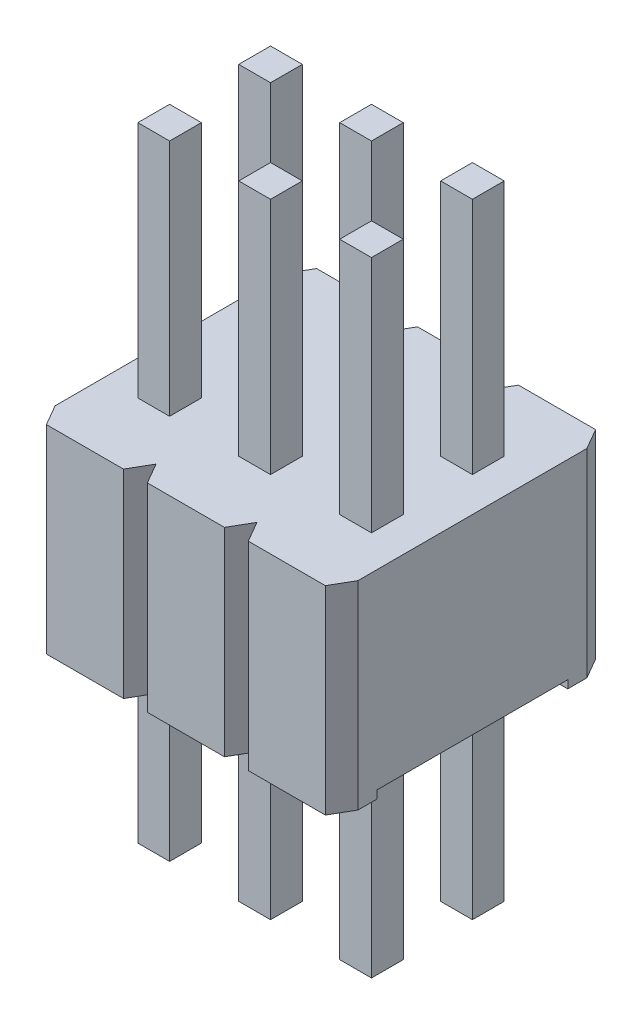
SolidWorks part; units mm, degrees
ref_plane "Front Plane" through (0, 0, 0) normal (0, 0, 1) x (1, 0, 0)
ref_plane "Top Plane" through (0, 0, 0) normal (0, 1, 0) x (1, 0, 0)
ref_plane "Right Plane" through (0, 0, 0) normal (1, 0, 0) x (0, 0, -1)
ref_plane "Plane1" through (0, 2.5, 0) normal (0, 1, 0) x (1, 0, 0)
sketch "Sketch1" plane through (0, 2.5, 0) normal (0, 1, 0) x (1, 0, 0)
  line L0 (3.175, -1.7) -> (3.175, 1.7)
  line L1 (3.175, 1.7) -> (-0.635, 1.7)
  line L2 (-0.635, 1.7) -> (-0.635, -1.7)
  line L3 (-0.635, -1.7) -> (3.175, -1.7)
extrude "Boss-Extrude1" add sketch "Sketch1" against normal blind 2.5
sketch "Sketch2" plane through (0, 0, 0) normal (0, -1, 0) x (1, 0, 0)
  line L0 (0.785, 1.7) -> (0.485, 1.7)
  line L1 (0.485, 1.7) -> (0.635, 1.44)
  line L2 (0.635, 1.44) -> (0.785, 1.7)
extrude "Cut-Extrude1" cut sketch "Sketch2" against normal blind 2.5
sketch "Sketch3" plane through (0, 0, 0) normal (0, -1, 0) x (1, 0, 0)
  line L0 (1.755, -1.7) -> (2.055, -1.7)
  line L1 (2.055, -1.7) -> (1.905, -1.44)
  line L2 (1.905, -1.44) -> (1.755, -1.7)
extrude "Cut-Extrude2" cut sketch "Sketch3" against normal blind 2.5
sketch "Sketch4" plane through (0, 0, 0) normal (0, -1, 0) x (1, 0, 0)
  line L0 (0.485, -1.7) -> (0.785, -1.7)
  line L1 (0.785, -1.7) -> (0.635, -1.44)
  line L2 (0.635, -1.44) -> (0.485, -1.7)
extrude "Cut-Extrude3" cut sketch "Sketch4" against normal blind 2.5
sketch "Sketch5" plane through (3.175, 0, 0) normal (1, 0, 0) x (0, 0, -1)
  line L0 (1.2, 0) -> (1.2, 0.1)
  line L1 (1.2, 0.1) -> (-1.2, 0.1)
  line L2 (-1.2, 0.1) -> (-1.2, 0)
  line L3 (-1.2, 0) -> (1.2, 0)
extrude "Cut-Extrude4" cut sketch "Sketch5" against normal through all
sketch "Sketch6" plane through (0, 0, 0) normal (0, -1, 0) x (1, 0, 0)
  line L0 (2.055, 1.7) -> (1.755, 1.7)
  line L1 (1.755, 1.7) -> (1.905, 1.44)
  line L2 (1.905, 1.44) -> (2.055, 1.7)
extrude "Cut-Extrude5" cut sketch "Sketch6" against normal blind 2.5
sketch "Sketch7" plane through (0, 0.1, 0) normal (0, -1, 0) x (1, 0, 0)
  line L0 (2.34, 0.835) -> (2.74, 0.835)
  line L1 (2.74, 0.835) -> (2.74, 0.435)
  line L2 (2.74, 0.435) -> (2.34, 0.435)
  line L3 (2.34, 0.435) -> (2.34, 0.835)
extrude "Boss-Extrude2" add sketch "Sketch7" along normal blind 2.45
sketch "Sketch8" plane through (0, 0.1, 0) normal (0, -1, 0) x (1, 0, 0)
  line L0 (2.34, -0.835) -> (2.34, -0.435)
  line L1 (2.34, -0.435) -> (2.74, -0.435)
  line L2 (2.74, -0.435) -> (2.74, -0.835)
  line L3 (2.74, -0.835) -> (2.34, -0.835)
extrude "Boss-Extrude3" add sketch "Sketch8" along normal blind 2.45
sketch "Sketch9" plane through (0, 0.1, 0) normal (0, -1, 0) x (1, 0, 0)
  line L0 (1.07, 0.835) -> (1.47, 0.835)
  line L1 (1.47, 0.835) -> (1.47, 0.435)
  line L2 (1.47, 0.435) -> (1.07, 0.435)
  line L3 (1.07, 0.435) -> (1.07, 0.835)
extrude "Boss-Extrude4" add sketch "Sketch9" along normal blind 2.45
sketch "Sketch10" plane through (0, 0.1, 0) normal (0, -1, 0) x (1, 0, 0)
  line L0 (1.07, -0.835) -> (1.07, -0.435)
  line L1 (1.07, -0.435) -> (1.47, -0.435)
  line L2 (1.47, -0.435) -> (1.47, -0.835)
  line L3 (1.47, -0.835) -> (1.07, -0.835)
extrude "Boss-Extrude5" add sketch "Sketch10" along normal blind 2.45
sketch "Sketch11" plane through (0, 0.1, 0) normal (0, -1, 0) x (1, 0, 0)
  line L0 (-0.2, 0.835) -> (0.2, 0.835)
  line L1 (0.2, 0.835) -> (0.2, 0.435)
  line L2 (0.2, 0.435) -> (-0.2, 0.435)
  line L3 (-0.2, 0.435) -> (-0.2, 0.835)
extrude "Boss-Extrude6" add sketch "Sketch11" along normal blind 2.45
sketch "Sketch12" plane through (0, 0.1, 0) normal (0, -1, 0) x (1, 0, 0)
  line L0 (-0.2, -0.835) -> (-0.2, -0.435)
  line L1 (-0.2, -0.435) -> (0.2, -0.435)
  line L2 (0.2, -0.435) -> (0.2, -0.835)
  line L3 (0.2, -0.835) -> (-0.2, -0.835)
extrude "Boss-Extrude7" add sketch "Sketch12" along normal blind 2.45
sketch "Sketch13" plane through (0, 2.5, 0) normal (0, 1, 0) x (-1, 0, 0)
  line L0 (-2.74, 0.835) -> (-2.34, 0.835)
  line L1 (-2.34, 0.835) -> (-2.34, 0.435)
  line L2 (-2.34, 0.435) -> (-2.74, 0.435)
  line L3 (-2.74, 0.435) -> (-2.74, 0.835)
extrude "Boss-Extrude8" add sketch "Sketch13" along normal blind 3
sketch "Sketch14" plane through (0, 2.5, 0) normal (0, 1, 0) x (-1, 0, 0)
  line L0 (-2.34, -0.435) -> (-2.34, -0.835)
  line L1 (-2.34, -0.835) -> (-2.74, -0.835)
  line L2 (-2.74, -0.835) -> (-2.74, -0.435)
  line L3 (-2.74, -0.435) -> (-2.34, -0.435)
extrude "Boss-Extrude9" add sketch "Sketch14" along normal blind 3
sketch "Sketch15" plane through (0, 2.5, 0) normal (0, 1, 0) x (-1, 0, 0)
  line L0 (-1.47, 0.835) -> (-1.07, 0.835)
  line L1 (-1.07, 0.835) -> (-1.07, 0.435)
  line L2 (-1.07, 0.435) -> (-1.47, 0.435)
  line L3 (-1.47, 0.435) -> (-1.47, 0.835)
extrude "Boss-Extrude10" add sketch "Sketch15" along normal blind 3
sketch "Sketch16" plane through (0, 2.5, 0) normal (0, 1, 0) x (-1, 0, 0)
  line L0 (-1.07, -0.435) -> (-1.07, -0.835)
  line L1 (-1.07, -0.835) -> (-1.47, -0.835)
  line L2 (-1.47, -0.835) -> (-1.47, -0.435)
  line L3 (-1.47, -0.435) -> (-1.07, -0.435)
extrude "Boss-Extrude11" add sketch "Sketch16" along normal blind 3
sketch "Sketch17" plane through (0, 2.5, 0) normal (0, 1, 0) x (-1, 0, 0)
  line L0 (-0.2, 0.835) -> (0.2, 0.835)
  line L1 (0.2, 0.835) -> (0.2, 0.435)
  line L2 (0.2, 0.435) -> (-0.2, 0.435)
  line L3 (-0.2, 0.435) -> (-0.2, 0.835)
extrude "Boss-Extrude12" add sketch "Sketch17" along normal blind 3
sketch "Sketch18" plane through (0, 2.5, 0) normal (0, 1, 0) x (-1, 0, 0)
  line L0 (0.2, -0.435) -> (0.2, -0.835)
  line L1 (0.2, -0.835) -> (-0.2, -0.835)
  line L2 (-0.2, -0.835) -> (-0.2, -0.435)
  line L3 (-0.2, -0.435) -> (0.2, -0.435)
extrude "Boss-Extrude13" add sketch "Sketch18" along normal blind 3
chamfer "Chamfer1" distance 0.15 angle 60.018 2 edges at (-0.635, 1.25, 1.7) (3.175, 1.25, -1.7)
chamfer "Chamfer2" distance 0.26 angle 29.982 2 edges at (3.175, 1.25, 1.7) (-0.635, 1.25, -1.7)
